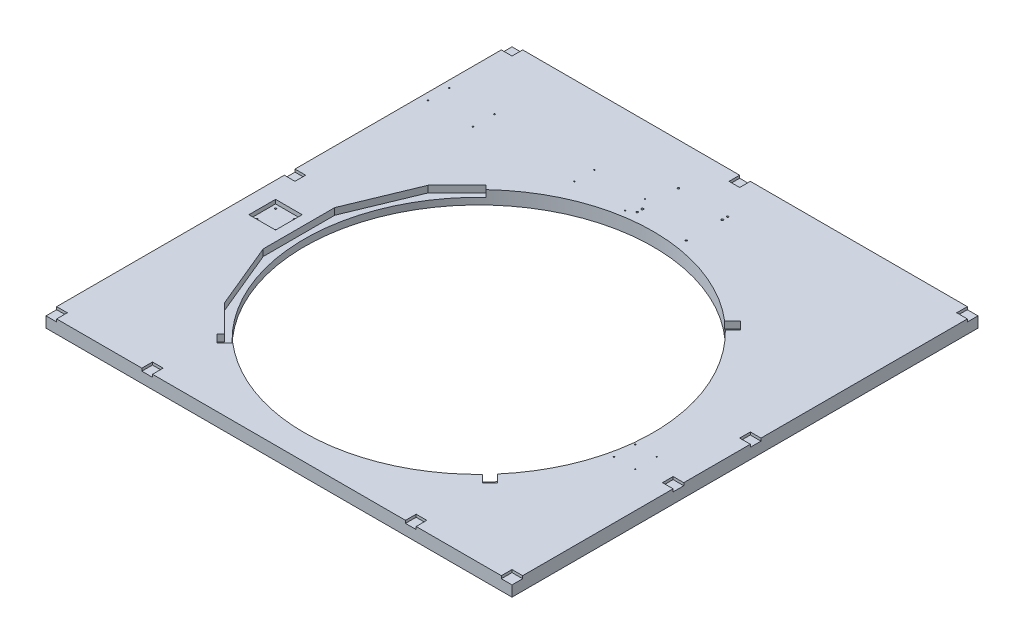
SolidWorks part; units mm, degrees
material "3003 Alloy"
ref_plane "Front Plane" through (0, 0, 0) normal (0, 0, 1) x (1, 0, 0)
ref_plane "Top Plane" through (0, 0, 0) normal (0, 1, 0) x (1, 0, 0)
ref_plane "Right Plane" through (0, 0, 0) normal (1, 0, 0) x (0, 0, -1)
sketch "Sketch1" plane through (0, 0, 0) normal (0, 1, 0) x (1, 0, 0)
  line L1 (-1000, -1000) -> (1000, -1000)
  line L2 (-1000, -1000) -> (-1000, 1000)
  line L3 (-1000, 1000) -> (1000, 1000)
  line L4 (1000, -1000) -> (1000, 1000)
  line L5 (-1000, -1000) -> (1000, 1000) construction
  line L6 (-1000, 1000) -> (1000, -1000) construction
  point P0 (0, 0)
  dimension "D1" = 2000
  dimension "D2" = 2000
extrude "Boss-Extrude1" add sketch "Sketch1" against normal blind 50
sketch "Sketch2" plane through (0, 0, 0) normal (0, 1, 0) x (1, 0, 0)
  circle A1 centre (0, -175) radius 6
  circle A3 centre (106, 129) radius 6
  dimension "D1" = 12
  dimension "D3" = 129
  dimension "D2" = 106
  dimension "D4" = 175
extrude "Cut-Extrude1" cut sketch "Sketch2" against normal blind 30
sketch "Sketch3" plane through (0, 0, 1000) normal (0, 0, 1) x (1, 0, 0)
  line L1 (-1000, 0) -> (1000, 0)
  line L2 (-1000, 0) -> (-1000, -50)
  line L3 (-1000, -50) -> (1000, -50)
  line L4 (1000, 0) -> (1000, -50)
extrude "Cut-Extrude2" cut sketch "Sketch3" against normal blind 250
sketch "Sketch4" plane through (-1000, 0, 0) normal (-1, 0, 0) x (0, 0, 1)
  line L1 (-1000, 0) -> (750, 0)
  line L2 (-1000, 0) -> (-1000, -50)
  line L3 (-1000, -50) -> (750, -50)
  line L4 (750, 0) -> (750, -50)
extrude "Cut-Extrude3" cut sketch "Sketch4" against normal blind 125
sketch "Sketch5" plane through (1000, 0, 0) normal (1, 0, 0) x (0, 0, -1)
  line L1 (-750, 0) -> (1000, 0)
  line L2 (-750, 0) -> (-750, -50)
  line L3 (-750, -50) -> (1000, -50)
  line L4 (1000, 0) -> (1000, -50)
extrude "Cut-Extrude4" cut sketch "Sketch5" against normal blind 125
sketch "Sketch6" plane through (0, 0, 0) normal (0, 1, 0) x (1, 0, 0)
  circle A0 centre (0, 0) radius 655
  dimension "D1" = 1310
extrude "Cut-Extrude5" cut sketch "Sketch6" against normal through all contours A0
sketch "Sketch7" plane through (0, 0, 0) normal (0, 1, 0) x (1, 0, 0)
  line L0 (0, 0) -> (-875, 0) construction
  line L1 (-875, -750) -> (-875, 1000) construction
  line L3 (-813, 50) -> (-713, 50)
  line L4 (-813, 50) -> (-813, -50)
  line L5 (-813, -50) -> (-713, -50)
  line L6 (-713, 50) -> (-713, -50)
  line L7 (-813, 50) -> (-713, -50) construction
  line L8 (-813, -50) -> (-713, 50) construction
  point P5 (-763, 0)
  dimension "D1" = 112
  dimension "D2" = 100
  dimension "D3" = 100
extrude "Cut-Extrude6" cut sketch "Sketch7" against normal blind 15
sketch "Sketch9" plane through (0, -15, 0) normal (0, 1, 0) x (1, 0, 0)
  line L0 (-713, -50) -> (-713, 50) construction
  line L1 (-813, -50) -> (-713, -50) construction
  line L2 (-713, 50) -> (-813, 50) construction
  line L3 (-813, 50) -> (-813, -50) construction
  circle A0 centre (-798, 35) radius 4
  circle A1 centre (-728, 35) radius 4
  circle A2 centre (-728, -35) radius 4
  circle A3 centre (-798, -35) radius 4
  dimension "D1" = 8
  dimension "D2" = 8
  dimension "D3" = 8
  dimension "D4" = 8
  dimension "D5" = 15
  dimension "D6" = 15
  dimension "D7" = 15
  dimension "D8" = 15
hole_wizard "M8 Tapped Hole1" positions "Sketch10" profile "Sketch11" tap size "M8" standard "ISO"
sketch "Sketch10" plane through (0, -15, 0) normal (0, 1, 0) x (1, 0, 0)
  point P0 (-798, 35)
  point P3 (-798, -35)
  point P6 (-728, -35)
  point P9 (-728, 35)
sketch "Sketch11" plane through (-798, -15, -35) normal (1, 0, 0) x (0, 0, 1)
  line L0 (0, 0) -> (0, 19.75)
  line L1 (0, 19.75) -> (3.4, 17.7071)
  line L2 (3.4, 17.7071) -> (3.4, 0)
  line L5 (3.4, 0) -> (0, 0)
  line L10 (0, 19.75) -> (-3.4, 17.7071) construction
  line L11 (0, -6.35) -> (0, 107.95) construction
  dimension "Tap Drill Dia." = 6.8
  dimension "Tap Drill Depth" = 19.75
  dimension "Drill Angle" = 118
cosmetic thread "Hole Thread1" parameters "D1"=16, "D2"=8
cosmetic thread "Hole Thread2" parameters "D1"=16, "D2"=8
cosmetic thread "Hole Thread3" parameters "D1"=16, "D2"=8
cosmetic thread "Hole Thread4" parameters "D1"=16, "D2"=8
sketch "Sketch13" plane through (0, -50, 0) normal (0, -1, 0) x (1, 0, 0)
  line L0 (875, 750) -> (875, -1000) construction
  line L1 (875, -1000) -> (-875, -1000) construction
  line L2 (-875, -1000) -> (-875, 750) construction
  line L3 (-875, 750) -> (875, 750) construction
  circle A0 centre (-835, 710) radius 15
  circle A1 centre (835, -960) radius 15
  circle A2 centre (835, 710) radius 15
  circle A3 centre (-835, -960) radius 15
  circle A4 centre (0, -960) radius 7.5
  circle A5 centre (0, 710) radius 7.5
  circle A6 centre (835, -125) radius 7.5
  circle A7 centre (-835, -125) radius 7.5
  dimension "D1" = 40
  dimension "D2" = 40
  dimension "D3" = 40
  dimension "D4" = 40
  dimension "D5" = 30
  dimension "D6" = 30
  dimension "D7" = 30
  dimension "D8" = 30
  dimension "D9" = 15
  dimension "D10" = 15
  dimension "D11" = 15
  dimension "D12" = 15
  dimension "D13" = 875
extrude "Cut-Extrude8" cut sketch "Sketch13" against normal blind 25
sketch "Sketch14" plane through (0, 0, 0) normal (0, 1, 0) x (1, 0, 0)
  line L0 (-875, -750) -> (-875, 1000) construction
  line L1 (875, -750) -> (835, -750)
  line L2 (875, -750) -> (875, -710)
  line L3 (875, -710) -> (835, -710)
  line L4 (835, -750) -> (835, -710)
  line L5 (835, 185) -> (915, 185)
  line L6 (835, 185) -> (835, 145)
  line L7 (835, 145) -> (915, 145)
  line L8 (915, 185) -> (915, 145)
  line L9 (835, 185) -> (915, 145) construction
  line L10 (835, 145) -> (915, 185) construction
  line L11 (875, 1000) -> (875, -750) construction
  line L12 (875, 1000) -> (835, 1000)
  line L13 (875, 1000) -> (875, 960)
  line L14 (875, 960) -> (835, 960)
  line L15 (835, 1000) -> (835, 960)
  line L16 (-875, 1000) -> (-835, 1000)
  line L17 (-875, 1000) -> (-875, 960)
  line L18 (-875, 960) -> (-835, 960)
  line L19 (-835, 1000) -> (-835, 960)
  line L20 (-875, -750) -> (-835, -750)
  line L21 (-875, -750) -> (-875, -710)
  line L22 (-875, -710) -> (-835, -710)
  line L23 (-835, -750) -> (-835, -710)
  line L24 (-835, 185) -> (-915, 185)
  line L25 (-835, 185) -> (-835, 145)
  line L26 (-835, 145) -> (-915, 145)
  line L27 (-915, 185) -> (-915, 145)
  line L28 (-835, 185) -> (-915, 145) construction
  line L29 (-835, 145) -> (-915, 185) construction
  line L30 (875, 1000) -> (-875, 1000) construction
  line L31 (-20, 1040) -> (20, 1040)
  line L32 (-20, 1040) -> (-20, 960)
  line L33 (-20, 960) -> (20, 960)
  line L34 (20, 1040) -> (20, 960)
  line L35 (-20, 1040) -> (20, 960) construction
  line L36 (-20, 960) -> (20, 1040) construction
  line L37 (875, -750) -> (-875, -750) construction
  line L39 (-515, -710) -> (-475, -710)
  line L40 (-515, -710) -> (-515, -790)
  line L41 (-515, -790) -> (-475, -790)
  line L42 (-475, -710) -> (-475, -790)
  line L43 (-515, -710) -> (-475, -790) construction
  line L44 (-515, -790) -> (-475, -710) construction
  line L45 (475, -710) -> (515, -710)
  line L46 (475, -710) -> (475, -790)
  line L47 (475, -790) -> (515, -790)
  line L48 (515, -710) -> (515, -790)
  line L49 (475, -710) -> (515, -790) construction
  line L50 (475, -790) -> (515, -710) construction
  line L51 (835, -105) -> (915, -105)
  line L52 (835, -105) -> (835, -145)
  line L53 (835, -145) -> (915, -145)
  line L54 (915, -105) -> (915, -145)
  line L55 (835, -105) -> (915, -145) construction
  line L56 (835, -145) -> (915, -105) construction
  point P5 (875, 165)
  point P28 (-875, 165)
  point P35 (0, 1000)
  point P44 (-495, -750)
  point P49 (495, -750)
  point P64 (875, -125)
  dimension "D1" = 40
  dimension "D2" = 40
  dimension "D3" = 40
  dimension "D4" = 80
  dimension "D5" = 40
  dimension "D6" = 40
  dimension "D7" = 40
  dimension "D8" = 40
  dimension "D9" = 40
  dimension "D10" = 80
  dimension "D11" = 80
  dimension "D12" = 40
  dimension "D13" = 40
  dimension "D14" = 80
  dimension "D15" = 80
  dimension "D16" = 40
  dimension "D17" = 320
  dimension "D18" = 320
  dimension "D19" = 895
  dimension "D20" = 80
  dimension "D21" = 40
  dimension "D22" = 250
extrude "Cut-Extrude9" cut sketch "Sketch14" against normal blind 10
sketch "Sketch15" plane through (0, 0, 0) normal (0, 1, 0) x (1, 0, 0)
  point P0 (660, -72)
  point P1 (660, -152)
  point P2 (740, -152)
  point P3 (740, -72)
hole_wizard "M5 Tapped Hole1" positions "Sketch16" profile "Sketch17" tap size "M5" standard "ISO"
sketch "Sketch16" plane through (0, 0, 0) normal (0, 1, 0) x (1, 0, 0)
  point P0 (740, -152)
  point P2 (740, -72)
  point P4 (660, -72)
  point P6 (660, -152)
  point P11 (-310.0912, 744.682)
  point P13 (-310.0912, 669.682)
  point P15 (-120.0912, 669.682)
  point P17 (-120.0912, 744.682)
sketch "Sketch17" plane through (740, 0, 152) normal (1, 0, 0) x (0, 0, 1)
  line L0 (0, 0) -> (0, 13.6618)
  line L1 (0, 13.6618) -> (2.1, 12.4)
  line L2 (2.1, 12.4) -> (2.1, 0)
  line L5 (2.1, 0) -> (0, 0)
  line L10 (0, 13.6618) -> (-2.1, 12.4) construction
  line L11 (0, -6.35) -> (0, 107.95) construction
  dimension "Tap Drill Dia." = 4.2
  dimension "Tap Drill Depth" = 12.4
  dimension "Drill Angle" = 118
cosmetic thread "Hole Thread5" parameters "D1"=10, "D2"=5
cosmetic thread "Hole Thread6" parameters "D1"=10, "D2"=5
cosmetic thread "Hole Thread7" parameters "D1"=10, "D2"=5
cosmetic thread "Hole Thread8" parameters "D1"=10, "D2"=5
cosmetic thread "Hole Thread13" parameters "D1"=10, "D2"=5
cosmetic thread "Hole Thread14" parameters "D1"=10, "D2"=5
cosmetic thread "Hole Thread15" parameters "D1"=10, "D2"=5
cosmetic thread "Hole Thread16" parameters "D1"=10, "D2"=5
sketch "Sketch18" plane through (0, 0, 0) normal (0, 1, 0) x (1, 0, 0)
  point P0 (-92.5, 687.5)
  point P1 (-92.5, 842.5)
  point P2 (92.5, 842.5)
  point P3 (92.5, 687.5)
hole_wizard "M8 Tapped Hole2" positions "Sketch19" profile "Sketch20" tap size "M8" standard "ISO"
sketch "Sketch19" plane through (0, 0, 0) normal (0, 1, 0) x (1, 0, 0)
  point P0 (-92.5, 687.5)
  point P2 (92.5, 687.5)
  point P4 (92.5, 842.5)
  point P6 (-92.5, 842.5)
sketch "Sketch20" plane through (-92.5, 0, -687.5) normal (1, 0, 0) x (0, 0, 1)
  line L0 (0, 0) -> (0, 21.7929)
  line L1 (0, 21.7929) -> (3.4, 19.75)
  line L2 (3.4, 19.75) -> (3.4, 0)
  line L5 (3.4, 0) -> (0, 0)
  line L10 (0, 21.7929) -> (-3.4, 19.75) construction
  line L11 (0, -6.35) -> (0, 107.95) construction
  dimension "Tap Drill Dia." = 6.8
  dimension "Tap Drill Depth" = 19.75
  dimension "Drill Angle" = 118
cosmetic thread "Hole Thread9" parameters "D1"=16, "D2"=8
cosmetic thread "Hole Thread10" parameters "D1"=16, "D2"=8
cosmetic thread "Hole Thread11" parameters "D1"=16, "D2"=8
cosmetic thread "Hole Thread12" parameters "D1"=16, "D2"=8
sketch "Sketch21" plane through (0, 0, 0) normal (0, 1, 0) x (1, 0, 0)
  circle A1 centre (-92.5, 707.5) radius 4
  circle A2 centre (92.5, 822.5) radius 4
  dimension "D1" = 8
  dimension "D2" = 8
extrude "Cut-Extrude10" cut sketch "Sketch21" against normal blind 10
sketch "Sketch22" plane through (0, 0, 0) normal (0, 1, 0) x (1, 0, 0)
  point P0 (-678.5, 738)
  point P1 (-678.5, 658)
  point P2 (-848.5, 658)
  point P3 (-848.5, 738)
hole_wizard "M6 Tapped Hole1" positions "Sketch23" profile "Sketch24" tap size "M6" standard "ISO"
sketch "Sketch23" plane through (0, 0, 0) normal (0, 1, 0) x (1, 0, 0)
  point P0 (-678.5, 738)
  point P2 (-678.5, 656.6044)
  point P4 (-848.5, 658)
  point P6 (-848.5, 738)
sketch "Sketch24" plane through (-678.5, 0, -738) normal (1, 0, 0) x (0, 0, 1)
  line L0 (0, 0) -> (0, 16.5022)
  line L1 (0, 16.5022) -> (2.5, 15)
  line L2 (2.5, 15) -> (2.5, 0)
  line L5 (2.5, 0) -> (0, 0)
  line L10 (0, 16.5022) -> (-2.5, 15) construction
  line L11 (0, -6.35) -> (0, 107.95) construction
  dimension "Tap Drill Dia." = 5
  dimension "Tap Drill Depth" = 15
  dimension "Drill Angle" = 118
cosmetic thread "Hole Thread17" parameters "D1"=12, "D2"=6
cosmetic thread "Hole Thread18" parameters "D1"=12, "D2"=6
cosmetic thread "Hole Thread19" parameters "D1"=12, "D2"=6
cosmetic thread "Hole Thread20" parameters "D1"=12, "D2"=6
sketch "Sketch25" plane through (0, 0, 0) normal (0, 1, 0) x (1, 0, 0)
  line L0 (0, 0) -> (-655, 0) construction
  line L1 (0, 0) -> (-605.1411, 250.6576) construction
  line L2 (0, 0) -> (-463.1549, 463.1549) construction
  line L3 (0, 0) -> (-605.1411, -250.6576) construction
  line L4 (0, 0) -> (-463.1549, -463.1549) construction
  line L5 (-572.2374, -382.3568) -> (-385.1698, -569.4243)
  line L6 (-555.2822, -371.0277) -> (-371.0277, -555.2822)
  line L7 (-655, -130.2876) -> (-555.2822, -371.0277)
  line L8 (-655, 130.2876) -> (-555.2822, 371.0277)
  line L9 (-555.2822, 371.0277) -> (-371.0277, 555.2822)
  line L10 (-675, -134.2658) -> (-572.2374, -382.3568)
  line L11 (-655, 130.2876) -> (-655, -130.2876)
  line L12 (-675, 134.2658) -> (-675, -134.2658)
  line L13 (-675, 134.2658) -> (-572.2374, 382.3568)
  line L14 (-572.2374, 382.3568) -> (-385.1698, 569.4243)
  line L15 (-470.226, -484.3681) -> (-425.27, -439.4121)
  line L16 (-463.1549, 491.4392) -> (-418.0254, 446.3097)
  circle A0 centre (0, 0) radius 611.5043
  point P11 (-655, 235.6482)
  point P14 (-463.1549, -463.1549)
  point P19 (-605.1411, -250.6576)
  point P20 (-463.1549, 463.1549)
  point P26 (-605.1411, 250.6576)
  dimension "D5" = 20
  dimension "D1" = 22.5
  dimension "D2" = 22.5
  dimension "D3" = 22.5
  dimension "D4" = 22.5
  dimension "D6" = 10
extrude "Cut-Extrude11" cut sketch "Sketch25" against normal blind 25 contours A0 L16 L9 L8 L11 L7 L6 L15 | L16 L14 L13 L12 L10 L5 L15 L6 L7 L11 L8 L9
sketch "Sketch26" plane through (0, 0, 0) normal (0, 1, 0) x (1, 0, 0)
  line L0 (-484.3681, -498.5103) -> (-456.0839, -470.226)
  line L13 (526.7946, -456.0839) -> (491.2875, -420.5768)
  line L29 (491.2875, -420.5768) -> (470.226, -456.0839)
  line L30 (-470.226, -484.3681) -> (-456.0299, -470.172) construction
  line L31 (498.5103, -484.3681) -> (470.226, -456.0839)
  line L32 (-484.3681, -498.5103) -> (-456.0839, -526.7946)
  line L33 (-456.0839, -526.7946) -> (-420.5768, -491.2875)
  line L34 (-420.5768, -491.2875) -> (-456.0839, -470.226)
  line L35 (498.5103, -484.3681) -> (526.7946, -456.0839)
  line L36 (456.0839, 526.7946) -> (420.5768, 491.2875)
  line L37 (420.5768, 491.2875) -> (456.0839, 470.226)
  line L38 (484.3681, 498.5103) -> (456.0839, 470.226)
  line L39 (484.3681, 498.5103) -> (456.0839, 526.7946)
  line L40 (0, 0) -> (-420.5768, -491.2875) construction
  line L41 (0, 0) -> (491.2875, -420.5768) construction
  point P4 (-470.226, -484.3681)
  dimension "D1" = 40
  dimension "D2" = 3
  dimension "D3" = 90
extrude "Cut-Extrude12" cut sketch "Sketch26" against normal blind 25
